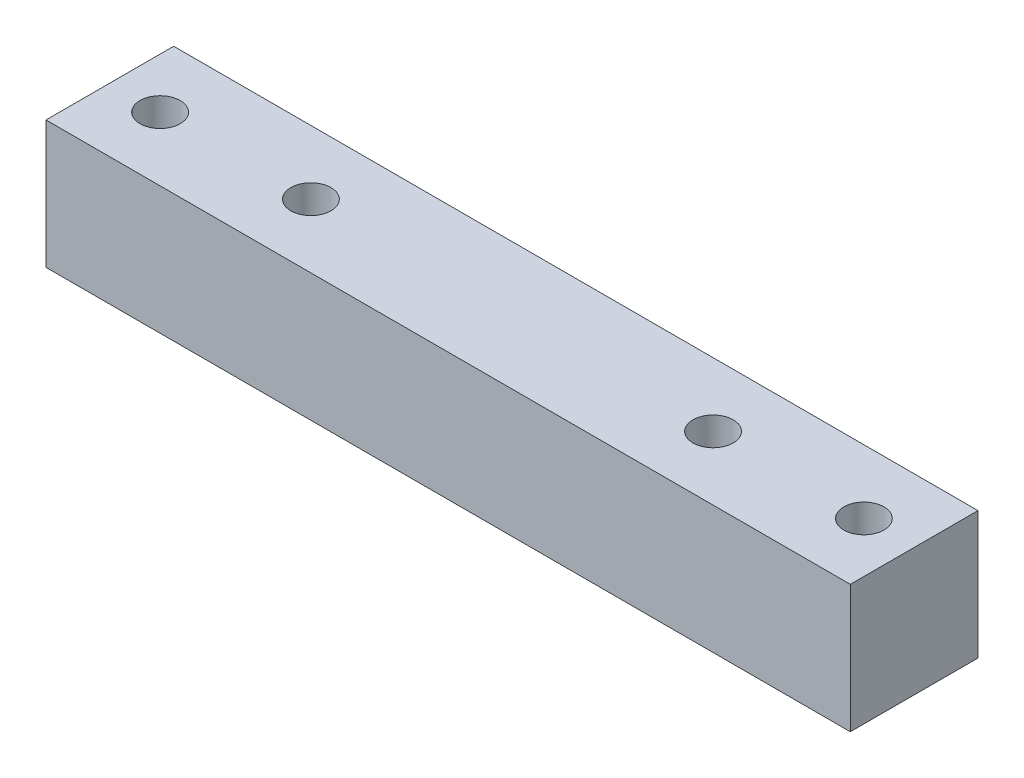
SolidWorks part; units mm, degrees
ref_plane "Front Plane" through (0, 0, 0) normal (0, 0, 1) x (1, 0, 0)
ref_plane "Top Plane" through (0, 0, 0) normal (0, 1, 0) x (1, 0, 0)
ref_plane "Right Plane" through (0, 0, 0) normal (1, 0, 0) x (0, 0, -1)
sketch "Sketch1" plane through (0, 0, 0) normal (0, 1, 0) x (1, 0, 0)
  line L0 (-40, 0) -> (40, 0) construction
  line L1 (40, -6.35) -> (-40, -6.35)
  line L2 (40, -6.35) -> (40, 6.35)
  line L3 (40, 6.35) -> (-40, 6.35)
  line L4 (-40, -6.35) -> (-40, 6.35)
  line L5 (40, -6.35) -> (-40, 6.35) construction
  line L6 (40, 6.35) -> (-40, -6.35) construction
  circle A0 centre (-35, 0) radius 2
  circle A1 centre (35, 0) radius 2
  circle A2 centre (20, 0) radius 2
  circle A3 centre (-20, 0) radius 2
  point P0 (0, 0)
  dimension "D3" = 5
  dimension "D5" = 15
  dimension "D1" = 12.7
  dimension "D2" = 80
  dimension "D4" = 5
  dimension "D6" = 15
extrude "Boss-Extrude1" add sketch "Sketch1" along normal blind 12.7
